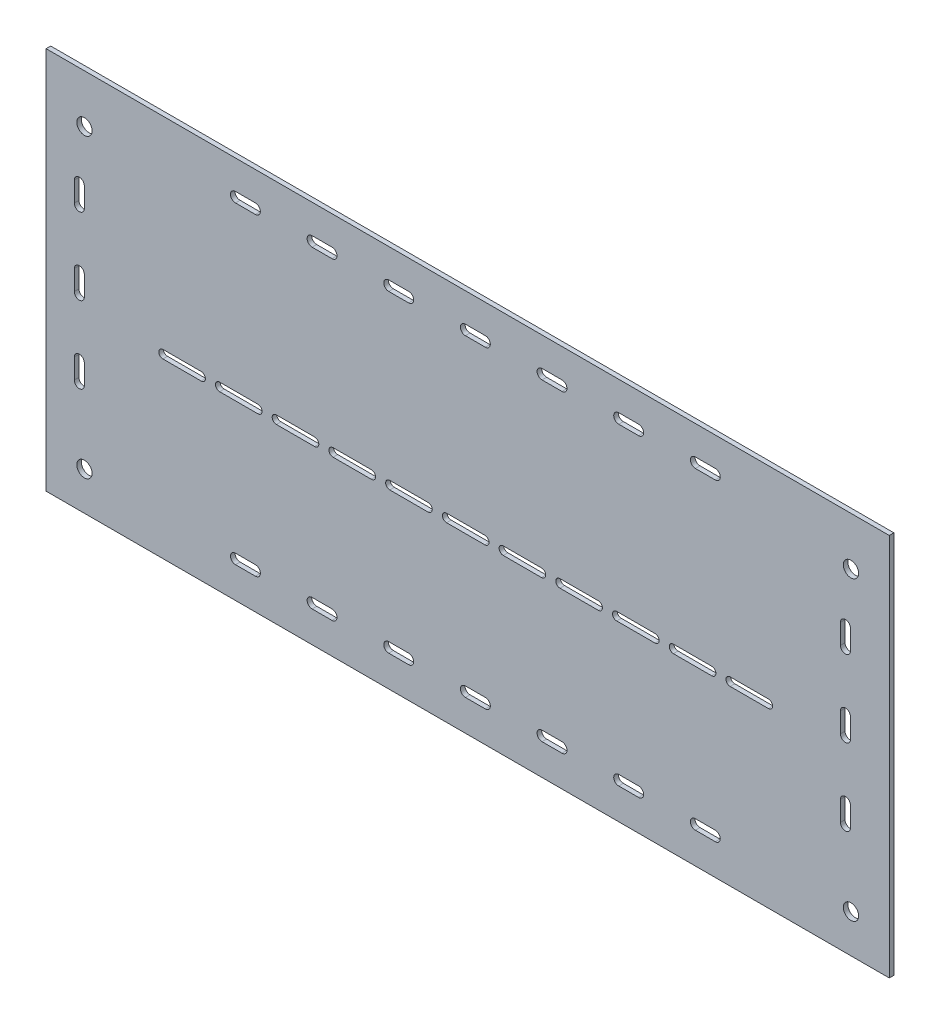
SolidWorks part; units mm, degrees
ref_plane "Alzado" through (0, 0, 0) normal (0, 0, 1) x (1, 0, 0)
ref_plane "Planta" through (0, 0, 0) normal (0, 1, 0) x (1, 0, 0)
ref_plane "Vista lateral" through (0, 0, 0) normal (1, 0, 0) x (0, 0, -1)
sketch "Croquis1" plane through (0, 0, 0) normal (0, 0, 1) x (1, 0, 0)
  line L1 (-275, 125) -> (275, 125)
  line L2 (-275, 125) -> (-275, -125)
  line L3 (-275, -125) -> (275, -125)
  line L4 (275, 125) -> (275, -125)
  line L5 (-275, 125) -> (275, -125) construction
  line L6 (-275, -125) -> (275, 125) construction
  point P0 (0, 0)
  dimension "D1" = 250
  dimension "D2" = 550
extrude "Saliente-Extruir1" add sketch "Croquis1" along normal blind 3
sketch "Croquis2" plane through (0, 0, 0) normal (0, 0, -1) x (-1, 0, 0)
  circle A0 centre (-250, -100) radius 5
  circle A1 centre (250, -100) radius 5
  circle A2 centre (250, 93.5) radius 5
  circle A4 centre (-250, 93.5) radius 5
  dimension "D1" = 10
  dimension "D2" = 10
  dimension "D3" = 10
  dimension "D4" = 10
extrude "Cortar-Extruir1" cut sketch "Croquis2" against normal through all
sketch "Croquis3" plane through (0, 0, 3) normal (0, 0, 1) x (1, 0, 0)
  line L2 (171.1819, -12.1945) -> (196.1819, -12.1945)
  line L3 (196.1819, -6.7945) -> (171.1819, -6.7945)
  line L4 (171.1819, -12.1945) -> (196.1819, -12.1945)
  line L5 (196.1819, -6.7945) -> (171.1819, -6.7945)
  line L6 (97.1819, -12.1945) -> (122.1819, -12.1945)
  line L7 (122.1819, -6.7945) -> (97.1819, -6.7945)
  line L8 (97.1819, -12.1945) -> (122.1819, -12.1945)
  line L9 (122.1819, -6.7945) -> (97.1819, -6.7945)
  line L10 (159.1819, -6.7945) -> (134.1819, -6.7945)
  line L11 (134.1819, -12.1945) -> (159.1819, -12.1945)
  line L12 (159.1819, -6.7945) -> (134.1819, -6.7945)
  line L13 (134.1819, -12.1945) -> (159.1819, -12.1945)
  line L14 (23.1819, -12.1945) -> (48.1819, -12.1945)
  line L15 (48.1819, -6.7945) -> (23.1819, -6.7945)
  line L16 (23.1819, -12.1945) -> (48.1819, -12.1945)
  line L17 (48.1819, -6.7945) -> (23.1819, -6.7945)
  line L18 (85.1819, -6.7945) -> (60.1819, -6.7945)
  line L19 (60.1819, -12.1945) -> (85.1819, -12.1945)
  line L20 (85.1819, -6.7945) -> (60.1819, -6.7945)
  line L21 (60.1819, -12.1945) -> (85.1819, -12.1945)
  line L22 (-101.5, 99.605) -> (-88.5, 99.605)
  line L23 (-88.5, 106.105) -> (-101.5, 106.105)
  line L24 (-101.5, 99.605) -> (-88.5, 99.605)
  line L25 (-88.5, 106.105) -> (-101.5, 106.105)
  line L26 (-138.5, 106.105) -> (-151.5, 106.105)
  line L27 (-151.5, 99.605) -> (-138.5, 99.605)
  line L28 (-138.5, 106.105) -> (-151.5, 106.105)
  line L29 (-151.5, 99.605) -> (-138.5, 99.605)
  line L30 (-1.5, 99.605) -> (11.5, 99.605)
  line L31 (11.5, 106.105) -> (-1.5, 106.105)
  line L32 (-1.5, 99.605) -> (11.5, 99.605)
  line L33 (11.5, 106.105) -> (-1.5, 106.105)
  line L34 (-38.5, 106.105) -> (-51.5, 106.105)
  line L35 (-51.5, 99.605) -> (-38.5, 99.605)
  line L36 (-38.5, 106.105) -> (-51.5, 106.105)
  line L37 (-51.5, 99.605) -> (-38.5, 99.605)
  line L38 (98.5, 99.605) -> (111.5, 99.605)
  line L39 (111.5, 106.105) -> (98.5, 106.105)
  line L40 (98.5, 99.605) -> (111.5, 99.605)
  line L41 (111.5, 106.105) -> (98.5, 106.105)
  line L42 (61.5, 106.105) -> (48.5, 106.105)
  line L43 (48.5, 99.605) -> (61.5, 99.605)
  line L44 (61.5, 106.105) -> (48.5, 106.105)
  line L45 (48.5, 99.605) -> (61.5, 99.605)
  line L46 (249.6493, 47) -> (249.6493, 60)
  line L47 (243.1493, 60) -> (243.1493, 47)
  line L48 (249.6493, 47) -> (249.6493, 60)
  line L49 (243.1493, 60) -> (243.1493, 47)
  line L50 (161.5, 106.105) -> (148.5, 106.105)
  line L51 (148.5, 99.605) -> (161.5, 99.605)
  line L52 (161.5, 106.105) -> (148.5, 106.105)
  line L53 (148.5, 99.605) -> (161.5, 99.605)
  line L54 (243.1493, -40) -> (243.1493, -53)
  line L55 (249.6493, -53) -> (249.6493, -40)
  line L56 (243.1493, -40) -> (243.1493, -53)
  line L57 (249.6493, -53) -> (249.6493, -40)
  line L58 (243.1493, 10) -> (243.1493, -3)
  line L59 (249.6493, -3) -> (249.6493, 10)
  line L60 (243.1493, 10) -> (243.1493, -3)
  line L61 (249.6493, -3) -> (249.6493, 10)
  line L62 (98.5, -104.75) -> (111.5, -104.75)
  line L63 (111.5, -98.25) -> (98.5, -98.25)
  line L64 (98.5, -104.75) -> (111.5, -104.75)
  line L65 (111.5, -98.25) -> (98.5, -98.25)
  line L66 (161.5, -98.25) -> (148.5, -98.25)
  line L67 (148.5, -104.75) -> (161.5, -104.75)
  line L68 (161.5, -98.25) -> (148.5, -98.25)
  line L69 (148.5, -104.75) -> (161.5, -104.75)
  line L70 (-1.5, -104.75) -> (11.5, -104.75)
  line L71 (11.5, -98.25) -> (-1.5, -98.25)
  line L72 (-1.5, -104.75) -> (11.5, -104.75)
  line L73 (11.5, -98.25) -> (-1.5, -98.25)
  line L74 (61.5, -98.25) -> (48.5, -98.25)
  line L75 (48.5, -104.75) -> (61.5, -104.75)
  line L76 (61.5, -98.25) -> (48.5, -98.25)
  line L77 (48.5, -104.75) -> (61.5, -104.75)
  line L78 (-50.8181, -12.1945) -> (-25.8181, -12.1945)
  line L79 (-25.8181, -6.7945) -> (-50.8181, -6.7945)
  line L80 (-50.8181, -12.1945) -> (-25.8181, -12.1945)
  line L81 (-25.8181, -6.7945) -> (-50.8181, -6.7945)
  line L82 (11.1819, -6.7945) -> (-13.8181, -6.7945)
  line L83 (-13.8181, -12.1945) -> (11.1819, -12.1945)
  line L84 (11.1819, -6.7945) -> (-13.8181, -6.7945)
  line L85 (-13.8181, -12.1945) -> (11.1819, -12.1945)
  line L86 (-99.8181, -6.7945) -> (-124.8181, -6.7945)
  line L87 (-124.8181, -12.1945) -> (-99.8181, -12.1945)
  line L88 (-99.8181, -6.7945) -> (-124.8181, -6.7945)
  line L89 (-124.8181, -12.1945) -> (-99.8181, -12.1945)
  line L90 (-62.8181, -6.7945) -> (-87.8181, -6.7945)
  line L91 (-87.8181, -12.1945) -> (-62.8181, -12.1945)
  line L92 (-62.8181, -6.7945) -> (-87.8181, -6.7945)
  line L93 (-87.8181, -12.1945) -> (-62.8181, -12.1945)
  line L94 (-173.8181, -6.7945) -> (-198.8181, -6.7945)
  line L95 (-198.8181, -12.1945) -> (-173.8181, -12.1945)
  line L96 (-173.8181, -6.7945) -> (-198.8181, -6.7945)
  line L97 (-198.8181, -12.1945) -> (-173.8181, -12.1945)
  line L98 (-136.8181, -6.7945) -> (-161.8181, -6.7945)
  line L99 (-161.8181, -12.1945) -> (-136.8181, -12.1945)
  line L100 (-136.8181, -6.7945) -> (-161.8181, -6.7945)
  line L101 (-161.8181, -12.1945) -> (-136.8181, -12.1945)
  line L102 (-101.5, -104.75) -> (-88.5, -104.75)
  line L103 (-88.5, -98.25) -> (-101.5, -98.25)
  line L104 (-101.5, -104.75) -> (-88.5, -104.75)
  line L105 (-88.5, -98.25) -> (-101.5, -98.25)
  line L106 (-38.5, -98.25) -> (-51.5, -98.25)
  line L107 (-51.5, -104.75) -> (-38.5, -104.75)
  line L108 (-38.5, -98.25) -> (-51.5, -98.25)
  line L109 (-51.5, -104.75) -> (-38.5, -104.75)
  line L110 (-151.5, -104.75) -> (-138.5, -104.75)
  line L111 (-138.5, -98.25) -> (-151.5, -98.25)
  line L112 (-151.5, -104.75) -> (-138.5, -104.75)
  line L113 (-138.5, -98.25) -> (-151.5, -98.25)
  line L114 (-250.0961, 47) -> (-250.0961, 60)
  line L115 (-256.5961, 60) -> (-256.5961, 47)
  line L116 (-250.0961, 47) -> (-250.0961, 60)
  line L117 (-256.5961, 60) -> (-256.5961, 47)
  line L118 (-256.5961, 10) -> (-256.5961, -3)
  line L119 (-250.0961, -3) -> (-250.0961, 10)
  line L120 (-256.5961, 10) -> (-256.5961, -3)
  line L121 (-250.0961, -3) -> (-250.0961, 10)
  line L122 (-256.5961, -40) -> (-256.5961, -53)
  line L123 (-250.0961, -53) -> (-250.0961, -40)
  line L124 (-256.5961, -40) -> (-256.5961, -53)
  line L125 (-250.0961, -53) -> (-250.0961, -40)
  arc A2 (249.6493, 60) -> (243.1493, 60) centre (246.3993, 60) ccw
  arc A3 (196.1819, -12.1945) -> (198.8819, -9.4945) centre (196.1819, -9.4945) ccw
  arc A4 (198.8819, -9.4945) -> (196.1819, -6.7945) centre (196.1819, -9.4945) ccw
  arc A5 (171.1819, -6.7945) -> (171.1819, -12.1945) centre (171.1819, -9.4945) ccw
  arc A6 (196.1819, -12.1945) -> (198.8819, -9.4945) centre (196.1819, -9.4945) ccw
  arc A7 (198.8819, -9.4945) -> (196.1819, -6.7945) centre (196.1819, -9.4945) ccw
  arc A8 (171.1819, -6.7945) -> (171.1819, -12.1945) centre (171.1819, -9.4945) ccw
  arc A9 (122.1819, -12.1945) -> (124.8819, -9.4945) centre (122.1819, -9.4945) ccw
  arc A10 (124.8819, -9.4945) -> (122.1819, -6.7945) centre (122.1819, -9.4945) ccw
  arc A11 (97.1819, -6.7945) -> (97.1819, -12.1945) centre (97.1819, -9.4945) ccw
  arc A12 (122.1819, -12.1945) -> (124.8819, -9.4945) centre (122.1819, -9.4945) ccw
  arc A13 (124.8819, -9.4945) -> (122.1819, -6.7945) centre (122.1819, -9.4945) ccw
  arc A14 (97.1819, -6.7945) -> (97.1819, -12.1945) centre (97.1819, -9.4945) ccw
  arc A15 (134.1819, -6.7945) -> (134.1819, -12.1945) centre (134.1819, -9.4945) ccw
  arc A16 (161.8819, -9.4945) -> (159.1819, -6.7945) centre (159.1819, -9.4945) ccw
  arc A17 (159.1819, -12.1945) -> (161.8819, -9.4945) centre (159.1819, -9.4945) ccw
  arc A18 (134.1819, -6.7945) -> (134.1819, -12.1945) centre (134.1819, -9.4945) ccw
  arc A19 (161.8819, -9.4945) -> (159.1819, -6.7945) centre (159.1819, -9.4945) ccw
  arc A20 (159.1819, -12.1945) -> (161.8819, -9.4945) centre (159.1819, -9.4945) ccw
  arc A21 (48.1819, -12.1945) -> (50.8819, -9.4945) centre (48.1819, -9.4945) ccw
  arc A22 (50.8819, -9.4945) -> (48.1819, -6.7945) centre (48.1819, -9.4945) ccw
  arc A23 (23.1819, -6.7945) -> (23.1819, -12.1945) centre (23.1819, -9.4945) ccw
  arc A24 (48.1819, -12.1945) -> (50.8819, -9.4945) centre (48.1819, -9.4945) ccw
  arc A25 (50.8819, -9.4945) -> (48.1819, -6.7945) centre (48.1819, -9.4945) ccw
  arc A26 (23.1819, -6.7945) -> (23.1819, -12.1945) centre (23.1819, -9.4945) ccw
  arc A27 (60.1819, -6.7945) -> (60.1819, -12.1945) centre (60.1819, -9.4945) ccw
  arc A28 (87.8819, -9.4945) -> (85.1819, -6.7945) centre (85.1819, -9.4945) ccw
  arc A29 (85.1819, -12.1945) -> (87.8819, -9.4945) centre (85.1819, -9.4945) ccw
  arc A30 (60.1819, -6.7945) -> (60.1819, -12.1945) centre (60.1819, -9.4945) ccw
  arc A31 (87.8819, -9.4945) -> (85.1819, -6.7945) centre (85.1819, -9.4945) ccw
  arc A32 (85.1819, -12.1945) -> (87.8819, -9.4945) centre (85.1819, -9.4945) ccw
  arc A33 (-88.5, 99.605) -> (-85.25, 102.855) centre (-88.5, 102.855) ccw
  arc A34 (-85.25, 102.855) -> (-88.5, 106.105) centre (-88.5, 102.855) ccw
  arc A35 (-101.5, 106.105) -> (-101.5, 99.605) centre (-101.5, 102.855) ccw
  arc A36 (-88.5, 99.605) -> (-85.25, 102.855) centre (-88.5, 102.855) ccw
  arc A37 (-85.25, 102.855) -> (-88.5, 106.105) centre (-88.5, 102.855) ccw
  arc A38 (-101.5, 106.105) -> (-101.5, 99.605) centre (-101.5, 102.855) ccw
  arc A39 (-151.5, 106.105) -> (-151.5, 99.605) centre (-151.5, 102.855) ccw
  arc A40 (-135.25, 102.855) -> (-138.5, 106.105) centre (-138.5, 102.855) ccw
  arc A41 (-138.5, 99.605) -> (-135.25, 102.855) centre (-138.5, 102.855) ccw
  arc A42 (-151.5, 106.105) -> (-151.5, 99.605) centre (-151.5, 102.855) ccw
  arc A43 (-135.25, 102.855) -> (-138.5, 106.105) centre (-138.5, 102.855) ccw
  arc A44 (-138.5, 99.605) -> (-135.25, 102.855) centre (-138.5, 102.855) ccw
  arc A45 (11.5, 99.605) -> (14.75, 102.855) centre (11.5, 102.855) ccw
  arc A46 (14.75, 102.855) -> (11.5, 106.105) centre (11.5, 102.855) ccw
  arc A47 (-1.5, 106.105) -> (-1.5, 99.605) centre (-1.5, 102.855) ccw
  arc A48 (11.5, 99.605) -> (14.75, 102.855) centre (11.5, 102.855) ccw
  arc A49 (14.75, 102.855) -> (11.5, 106.105) centre (11.5, 102.855) ccw
  arc A50 (-1.5, 106.105) -> (-1.5, 99.605) centre (-1.5, 102.855) ccw
  arc A51 (-51.5, 106.105) -> (-51.5, 99.605) centre (-51.5, 102.855) ccw
  arc A52 (-35.25, 102.855) -> (-38.5, 106.105) centre (-38.5, 102.855) ccw
  arc A53 (-38.5, 99.605) -> (-35.25, 102.855) centre (-38.5, 102.855) ccw
  arc A54 (-51.5, 106.105) -> (-51.5, 99.605) centre (-51.5, 102.855) ccw
  arc A55 (-35.25, 102.855) -> (-38.5, 106.105) centre (-38.5, 102.855) ccw
  arc A56 (-38.5, 99.605) -> (-35.25, 102.855) centre (-38.5, 102.855) ccw
  arc A57 (111.5, 99.605) -> (114.75, 102.855) centre (111.5, 102.855) ccw
  arc A58 (114.75, 102.855) -> (111.5, 106.105) centre (111.5, 102.855) ccw
  arc A59 (98.5, 106.105) -> (98.5, 99.605) centre (98.5, 102.855) ccw
  arc A60 (111.5, 99.605) -> (114.75, 102.855) centre (111.5, 102.855) ccw
  arc A61 (114.75, 102.855) -> (111.5, 106.105) centre (111.5, 102.855) ccw
  arc A62 (98.5, 106.105) -> (98.5, 99.605) centre (98.5, 102.855) ccw
  arc A63 (48.5, 106.105) -> (48.5, 99.605) centre (48.5, 102.855) ccw
  arc A64 (64.75, 102.855) -> (61.5, 106.105) centre (61.5, 102.855) ccw
  arc A65 (61.5, 99.605) -> (64.75, 102.855) centre (61.5, 102.855) ccw
  arc A66 (48.5, 106.105) -> (48.5, 99.605) centre (48.5, 102.855) ccw
  arc A67 (64.75, 102.855) -> (61.5, 106.105) centre (61.5, 102.855) ccw
  arc A68 (61.5, 99.605) -> (64.75, 102.855) centre (61.5, 102.855) ccw
  arc A69 (243.1493, 47) -> (249.6493, 47) centre (246.3993, 47) ccw
  arc A70 (249.6493, 60) -> (243.1493, 60) centre (246.3993, 60) ccw
  arc A71 (243.1493, 47) -> (249.6493, 47) centre (246.3993, 47) ccw
  arc A72 (243.1493, -53) -> (249.6493, -53) centre (246.3993, -53) ccw
  arc A73 (148.5, 106.105) -> (148.5, 99.605) centre (148.5, 102.855) ccw
  arc A74 (164.75, 102.855) -> (161.5, 106.105) centre (161.5, 102.855) ccw
  arc A75 (161.5, 99.605) -> (164.75, 102.855) centre (161.5, 102.855) ccw
  arc A76 (148.5, 106.105) -> (148.5, 99.605) centre (148.5, 102.855) ccw
  arc A77 (164.75, 102.855) -> (161.5, 106.105) centre (161.5, 102.855) ccw
  arc A78 (161.5, 99.605) -> (164.75, 102.855) centre (161.5, 102.855) ccw
  arc A79 (249.6493, -40) -> (243.1493, -40) centre (246.3993, -40) ccw
  arc A80 (243.1493, -53) -> (249.6493, -53) centre (246.3993, -53) ccw
  arc A81 (249.6493, -40) -> (243.1493, -40) centre (246.3993, -40) ccw
  arc A82 (249.6493, 10) -> (243.1493, 10) centre (246.3993, 10) ccw
  arc A83 (243.1493, -3) -> (249.6493, -3) centre (246.3993, -3) ccw
  arc A84 (249.6493, 10) -> (243.1493, 10) centre (246.3993, 10) ccw
  arc A85 (243.1493, -3) -> (249.6493, -3) centre (246.3993, -3) ccw
  arc A86 (-250.0961, 60) -> (-256.5961, 60) centre (-253.3461, 60) ccw
  arc A87 (111.5, -104.75) -> (114.75, -101.5) centre (111.5, -101.5) ccw
  arc A88 (114.75, -101.5) -> (111.5, -98.25) centre (111.5, -101.5) ccw
  arc A89 (98.5, -98.25) -> (98.5, -104.75) centre (98.5, -101.5) ccw
  arc A90 (111.5, -104.75) -> (114.75, -101.5) centre (111.5, -101.5) ccw
  arc A91 (114.75, -101.5) -> (111.5, -98.25) centre (111.5, -101.5) ccw
  arc A92 (98.5, -98.25) -> (98.5, -104.75) centre (98.5, -101.5) ccw
  arc A93 (148.5, -98.25) -> (148.5, -104.75) centre (148.5, -101.5) ccw
  arc A94 (164.75, -101.5) -> (161.5, -98.25) centre (161.5, -101.5) ccw
  arc A95 (161.5, -104.75) -> (164.75, -101.5) centre (161.5, -101.5) ccw
  arc A96 (148.5, -98.25) -> (148.5, -104.75) centre (148.5, -101.5) ccw
  arc A97 (164.75, -101.5) -> (161.5, -98.25) centre (161.5, -101.5) ccw
  arc A98 (161.5, -104.75) -> (164.75, -101.5) centre (161.5, -101.5) ccw
  arc A99 (11.5, -104.75) -> (14.75, -101.5) centre (11.5, -101.5) ccw
  arc A100 (14.75, -101.5) -> (11.5, -98.25) centre (11.5, -101.5) ccw
  arc A101 (-1.5, -98.25) -> (-1.5, -104.75) centre (-1.5, -101.5) ccw
  arc A102 (11.5, -104.75) -> (14.75, -101.5) centre (11.5, -101.5) ccw
  arc A103 (14.75, -101.5) -> (11.5, -98.25) centre (11.5, -101.5) ccw
  arc A104 (-1.5, -98.25) -> (-1.5, -104.75) centre (-1.5, -101.5) ccw
  arc A105 (48.5, -98.25) -> (48.5, -104.75) centre (48.5, -101.5) ccw
  arc A106 (64.75, -101.5) -> (61.5, -98.25) centre (61.5, -101.5) ccw
  arc A107 (61.5, -104.75) -> (64.75, -101.5) centre (61.5, -101.5) ccw
  arc A108 (48.5, -98.25) -> (48.5, -104.75) centre (48.5, -101.5) ccw
  arc A109 (64.75, -101.5) -> (61.5, -98.25) centre (61.5, -101.5) ccw
  arc A110 (61.5, -104.75) -> (64.75, -101.5) centre (61.5, -101.5) ccw
  arc A111 (-25.8181, -12.1945) -> (-23.1181, -9.4945) centre (-25.8181, -9.4945) ccw
  arc A112 (-23.1181, -9.4945) -> (-25.8181, -6.7945) centre (-25.8181, -9.4945) ccw
  arc A113 (-50.8181, -6.7945) -> (-50.8181, -12.1945) centre (-50.8181, -9.4945) ccw
  arc A114 (-25.8181, -12.1945) -> (-23.1181, -9.4945) centre (-25.8181, -9.4945) ccw
  arc A115 (-23.1181, -9.4945) -> (-25.8181, -6.7945) centre (-25.8181, -9.4945) ccw
  arc A116 (-50.8181, -6.7945) -> (-50.8181, -12.1945) centre (-50.8181, -9.4945) ccw
  arc A117 (-13.8181, -6.7945) -> (-13.8181, -12.1945) centre (-13.8181, -9.4945) ccw
  arc A118 (13.8819, -9.4945) -> (11.1819, -6.7945) centre (11.1819, -9.4945) ccw
  arc A119 (11.1819, -12.1945) -> (13.8819, -9.4945) centre (11.1819, -9.4945) ccw
  arc A120 (-13.8181, -6.7945) -> (-13.8181, -12.1945) centre (-13.8181, -9.4945) ccw
  arc A121 (13.8819, -9.4945) -> (11.1819, -6.7945) centre (11.1819, -9.4945) ccw
  arc A122 (11.1819, -12.1945) -> (13.8819, -9.4945) centre (11.1819, -9.4945) ccw
  arc A123 (-124.8181, -6.7945) -> (-124.8181, -12.1945) centre (-124.8181, -9.4945) ccw
  arc A124 (-99.8181, -12.1945) -> (-97.1181, -9.4945) centre (-99.8181, -9.4945) ccw
  arc A125 (-97.1181, -9.4945) -> (-99.8181, -6.7945) centre (-99.8181, -9.4945) ccw
  arc A126 (-124.8181, -6.7945) -> (-124.8181, -12.1945) centre (-124.8181, -9.4945) ccw
  arc A127 (-99.8181, -12.1945) -> (-97.1181, -9.4945) centre (-99.8181, -9.4945) ccw
  arc A128 (-97.1181, -9.4945) -> (-99.8181, -6.7945) centre (-99.8181, -9.4945) ccw
  arc A129 (-87.8181, -6.7945) -> (-87.8181, -12.1945) centre (-87.8181, -9.4945) ccw
  arc A130 (-60.1181, -9.4945) -> (-62.8181, -6.7945) centre (-62.8181, -9.4945) ccw
  arc A131 (-62.8181, -12.1945) -> (-60.1181, -9.4945) centre (-62.8181, -9.4945) ccw
  arc A132 (-87.8181, -6.7945) -> (-87.8181, -12.1945) centre (-87.8181, -9.4945) ccw
  arc A133 (-60.1181, -9.4945) -> (-62.8181, -6.7945) centre (-62.8181, -9.4945) ccw
  arc A134 (-62.8181, -12.1945) -> (-60.1181, -9.4945) centre (-62.8181, -9.4945) ccw
  arc A135 (-198.8181, -6.7945) -> (-198.8181, -12.1945) centre (-198.8181, -9.4945) ccw
  arc A136 (-173.8181, -12.1945) -> (-171.1181, -9.4945) centre (-173.8181, -9.4945) ccw
  arc A137 (-171.1181, -9.4945) -> (-173.8181, -6.7945) centre (-173.8181, -9.4945) ccw
  arc A138 (-198.8181, -6.7945) -> (-198.8181, -12.1945) centre (-198.8181, -9.4945) ccw
  arc A139 (-173.8181, -12.1945) -> (-171.1181, -9.4945) centre (-173.8181, -9.4945) ccw
  arc A140 (-171.1181, -9.4945) -> (-173.8181, -6.7945) centre (-173.8181, -9.4945) ccw
  arc A141 (-161.8181, -6.7945) -> (-161.8181, -12.1945) centre (-161.8181, -9.4945) ccw
  arc A142 (-134.1181, -9.4945) -> (-136.8181, -6.7945) centre (-136.8181, -9.4945) ccw
  arc A143 (-136.8181, -12.1945) -> (-134.1181, -9.4945) centre (-136.8181, -9.4945) ccw
  arc A144 (-161.8181, -6.7945) -> (-161.8181, -12.1945) centre (-161.8181, -9.4945) ccw
  arc A145 (-134.1181, -9.4945) -> (-136.8181, -6.7945) centre (-136.8181, -9.4945) ccw
  arc A146 (-136.8181, -12.1945) -> (-134.1181, -9.4945) centre (-136.8181, -9.4945) ccw
  arc A147 (-88.5, -104.75) -> (-85.25, -101.5) centre (-88.5, -101.5) ccw
  arc A148 (-85.25, -101.5) -> (-88.5, -98.25) centre (-88.5, -101.5) ccw
  arc A149 (-101.5, -98.25) -> (-101.5, -104.75) centre (-101.5, -101.5) ccw
  arc A150 (-88.5, -104.75) -> (-85.25, -101.5) centre (-88.5, -101.5) ccw
  arc A151 (-85.25, -101.5) -> (-88.5, -98.25) centre (-88.5, -101.5) ccw
  arc A152 (-101.5, -98.25) -> (-101.5, -104.75) centre (-101.5, -101.5) ccw
  arc A153 (-51.5, -98.25) -> (-51.5, -104.75) centre (-51.5, -101.5) ccw
  arc A154 (-35.25, -101.5) -> (-38.5, -98.25) centre (-38.5, -101.5) ccw
  arc A155 (-38.5, -104.75) -> (-35.25, -101.5) centre (-38.5, -101.5) ccw
  arc A156 (-51.5, -98.25) -> (-51.5, -104.75) centre (-51.5, -101.5) ccw
  arc A157 (-35.25, -101.5) -> (-38.5, -98.25) centre (-38.5, -101.5) ccw
  arc A158 (-38.5, -104.75) -> (-35.25, -101.5) centre (-38.5, -101.5) ccw
  arc A159 (-138.5, -104.75) -> (-135.25, -101.5) centre (-138.5, -101.5) ccw
  arc A160 (-135.25, -101.5) -> (-138.5, -98.25) centre (-138.5, -101.5) ccw
  arc A161 (-151.5, -98.25) -> (-151.5, -104.75) centre (-151.5, -101.5) ccw
  arc A162 (-138.5, -104.75) -> (-135.25, -101.5) centre (-138.5, -101.5) ccw
  arc A163 (-135.25, -101.5) -> (-138.5, -98.25) centre (-138.5, -101.5) ccw
  arc A164 (-151.5, -98.25) -> (-151.5, -104.75) centre (-151.5, -101.5) ccw
  arc A165 (-256.5961, 47) -> (-250.0961, 47) centre (-253.3461, 47) ccw
  arc A166 (-250.0961, 60) -> (-256.5961, 60) centre (-253.3461, 60) ccw
  arc A167 (-256.5961, 47) -> (-250.0961, 47) centre (-253.3461, 47) ccw
  arc A168 (-256.5961, -3) -> (-250.0961, -3) centre (-253.3461, -3) ccw
  arc A169 (-250.0961, 10) -> (-256.5961, 10) centre (-253.3461, 10) ccw
  arc A170 (-256.5961, -3) -> (-250.0961, -3) centre (-253.3461, -3) ccw
  arc A171 (-250.0961, 10) -> (-256.5961, 10) centre (-253.3461, 10) ccw
  arc A172 (-250.0961, -40) -> (-256.5961, -40) centre (-253.3461, -40) ccw
  arc A173 (-256.5961, -53) -> (-250.0961, -53) centre (-253.3461, -53) ccw
  arc A174 (-250.0961, -40) -> (-256.5961, -40) centre (-253.3461, -40) ccw
  arc A175 (-256.5961, -53) -> (-250.0961, -53) centre (-253.3461, -53) ccw
  dimension "D1" = 0
  dimension "D2" = 0
  dimension "D3" = 0
  dimension "D4" = 0
  dimension "D5" = 0
  dimension "D6" = 0
  dimension "D7" = 0
  dimension "D8" = 0
  dimension "D9" = 0
  dimension "D10" = 0
  dimension "D11" = 0
  dimension "D12" = 0
  dimension "D13" = 0
  dimension "D14" = 0
  dimension "D15" = 0
  dimension "D16" = 0
  dimension "D17" = 0
  dimension "D18" = 0
  dimension "D19" = 0
  dimension "D20" = 0
  dimension "D21" = 0
  dimension "D22" = 0
  dimension "D23" = 0
  dimension "D24" = 0
  dimension "D25" = 0
  dimension "D26" = 0
  dimension "D27" = 0
  dimension "D28" = 0
  dimension "D29" = 0
  dimension "D30" = 0
  dimension "D31" = 0
extrude "Cortar-Extruir2" cut sketch "Croquis3" against normal through all
